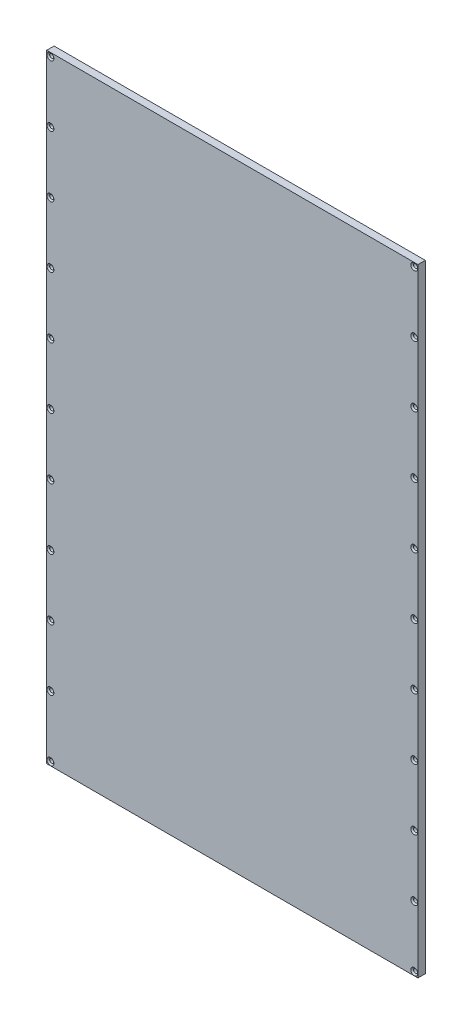
SolidWorks part; units mm, degrees
ref_plane "Front" through (0, 0, 0) normal (0, 0, 1) x (1, 0, 0)
ref_plane "Top" through (0, 0, 0) normal (0, 1, 0) x (1, 0, 0)
ref_plane "Right" through (0, 0, 0) normal (1, 0, 0) x (0, 0, -1)
sketch "Sketch1" plane through (0, 0, 0) normal (0, 0, 1) x (1, 0, 0)
  line L1 (0, 0) -> (304, 0)
  line L2 (0, 0) -> (0, 506)
  line L3 (0, 506) -> (304, 506)
  line L4 (304, 0) -> (304, 506)
  dimension "D1" = 304
  dimension "D2" = 506
extrude "Boss-Extrude1" add sketch "Sketch1" along normal blind 6
hole_wizard "CSK for #4 Flat Head Machine Screw (100)1" positions "Sketch2" profile "Sketch3" countersink size "#4" standard "ANSI Inch" end condition through all
sketch "Sketch2" plane through (0, 0, 6) normal (0, 0, 1) x (1, 0, 0)
  line L0 (3, 506) -> (3, 0) construction
  line L1 (304, 506) -> (0, 506) construction
  line L2 (0, 0) -> (304, 0) construction
  line L4 (0, 506) -> (0, 0) construction
  line L5 (152, 506) -> (152, 0) construction
  point P0 (3, 503)
  point P13 (3, 3)
  point P24 (3, 253)
  point P41 (3, 303)
  point P43 (3, 353)
  point P45 (3, 403)
  point P47 (3, 453)
  point P49 (3, 203)
  point P51 (3, 153)
  point P53 (3, 103)
  point P55 (3, 53)
  point P60 (301, 503)
  point P61 (301, 453)
  point P62 (301, 403)
  point P63 (301, 353)
  point P64 (301, 303)
  point P65 (301, 253)
  point P66 (301, 203)
  point P67 (301, 153)
  point P68 (301, 103)
  point P69 (301, 53)
  point P70 (301, 3)
  dimension "D1" = 3
  dimension "D2" = 3
  dimension "D3" = 3
  dimension "D4" = 50
  dimension "D5" = 50
  dimension "D6" = 50
  dimension "D7" = 50
  dimension "D8" = 50
  dimension "D9" = 50
  dimension "D10" = 50
  dimension "D11" = 50
sketch "Sketch3" plane through (3, 503, 6) normal (1, 0, 0) x (0, -1, 0)
  line L0 (0, 0) -> (0, 6)
  line L1 (0, 6) -> (1.6319, 6)
  line L2 (1.6319, 6) -> (1.6319, 1.0284)
  line L3 (1.6319, 1.0284) -> (2.8575, 0)
  line L5 (2.8575, 0) -> (0, 0)
  line L6 (-1.6319, 1.0284) -> (-2.8575, 0) construction
  line L11 (0, -6.35) -> (0, 107.95) construction
  dimension "Thru Hole Dia." = 3.2639
  dimension "Thru Hole Depth" = 6
  dimension "Near C'Sink Dia." = 5.715
  dimension "Near C'Sink Angle" = 100
equation "\"D5@Sketch2\"=\"D4@Sketch2\""
equation "\"D6@Sketch2\"=\"D4@Sketch2\""
equation "\"D7@Sketch2\"=\"D4@Sketch2\""
equation "\"D8@Sketch2\"=\"D4@Sketch2\""
equation "\"D9@Sketch2\"=\"D4@Sketch2\""
equation "\"D10@Sketch2\"=\"D4@Sketch2\""
equation "\"D11@Sketch2\"=\"D4@Sketch2\""
